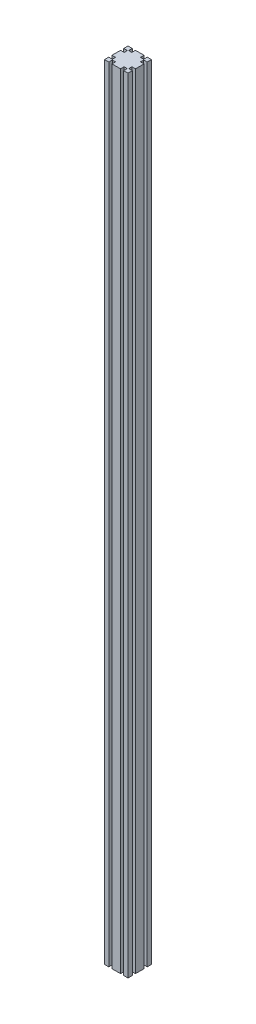
SolidWorks part; units mm, degrees
ref_plane "前视基准面" through (0, 0, 0) normal (0, 0, 1) x (1, 0, 0)
ref_plane "上视基准面" through (0, 0, 0) normal (0, 1, 0) x (1, 0, 0)
ref_plane "右视基准面" through (0, 0, 0) normal (1, 0, 0) x (0, 0, -1)
sketch "草图1" plane through (0, 0, 0) normal (0, 1, 0) x (1, 0, 0)
  line L0 (0, 60) -> (0, 49.1)
  line L1 (0, 0) -> (60, 0)
  line L2 (0, 0) -> (0, 60)
  line L3 (0, 60) -> (60, 60)
  line L4 (60, 0) -> (60, 60)
  line L5 (0, 0) -> (60, 60) construction
  line L6 (0, 60) -> (60, 0) construction
  line L7 (0, 49.1) -> (9.2, 49.1)
  line L8 (9.2, 49.1) -> (9.2, 40.9)
  line L9 (9.2, 40.9) -> (0, 40.9)
  line L10 (0, 30) -> (30, 30)
  line L11 (30, 30) -> (30, 60)
  line L12 (60, 49.1) -> (50.8, 49.1)
  line L13 (50.8, 49.1) -> (50.8, 40.9)
  line L14 (50.8, 40.9) -> (60, 40.9)
  line L15 (10.9, 0) -> (10.9, 9.2)
  line L16 (10.9, 9.2) -> (19.1, 9.2)
  line L17 (19.1, 9.2) -> (19.1, 0)
  line L18 (10.9, 50.8) -> (19.1, 50.8)
  line L19 (10.9, 60) -> (10.9, 50.8)
  line L20 (19.1, 50.8) -> (19.1, 60)
  line L21 (9.2, 19.1) -> (0, 19.1)
  line L22 (9.2, 10.9) -> (9.2, 19.1)
  line L23 (0, 10.9) -> (9.2, 10.9)
  line L24 (49.1, 60) -> (49.1, 50.8)
  line L25 (49.1, 50.8) -> (40.9, 50.8)
  line L26 (40.9, 50.8) -> (40.9, 60)
  line L27 (50.8, 19.1) -> (60, 19.1)
  line L28 (60, 10.9) -> (50.8, 10.9)
  line L29 (50.8, 10.9) -> (50.8, 19.1)
  line L30 (49.1, 9.2) -> (40.9, 9.2)
  line L31 (49.1, 0) -> (49.1, 9.2)
  line L32 (40.9, 9.2) -> (40.9, 0)
  point P4 (30, 30)
extrude "凸台-拉伸1" add sketch "草图1" along normal blind 2000 contours L20 L18 L19 L3 L0 L7 L8 L9 L2 L10 L11 | L32 L30 L31 L1 L4 L28 L29 L27 L14 L13 L12 L3 L24 L25 L26 L11 L10 L2 L21 L22 L23 L15 L16 L17
